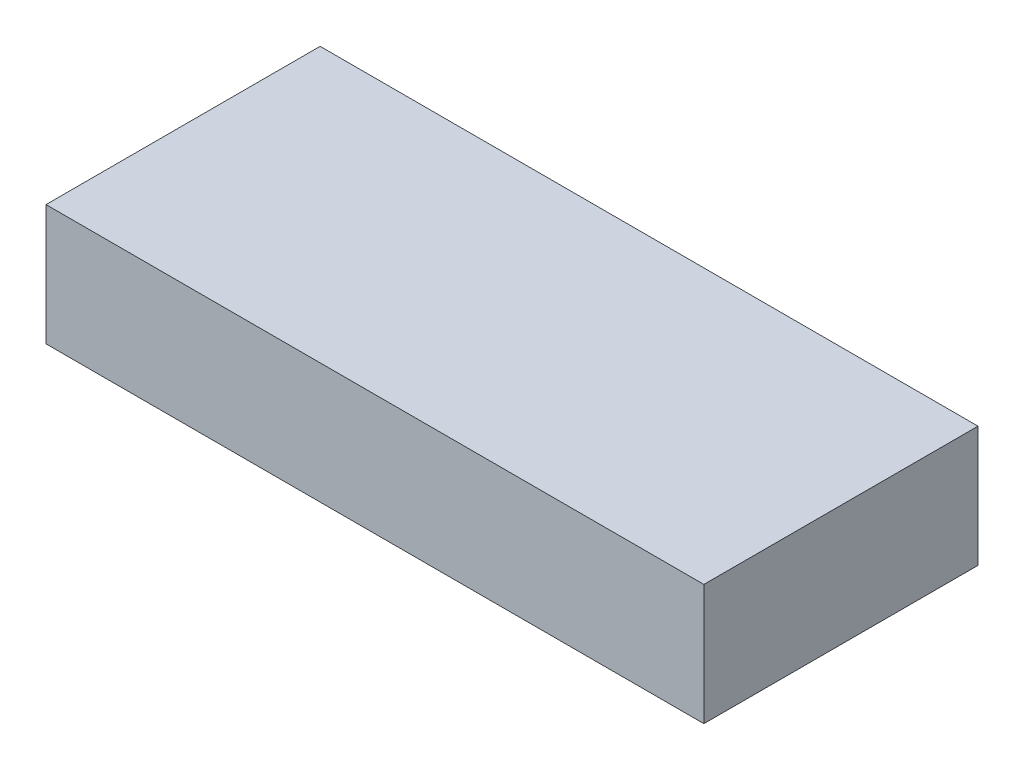
SolidWorks part; units mm, degrees
ref_plane "Front" through (0, 0, 0) normal (0, 0, 1) x (1, 0, 0)
ref_plane "Top" through (0, 0, 0) normal (0, 1, 0) x (1, 0, 0)
ref_plane "Right" through (0, 0, 0) normal (1, 0, 0) x (0, 0, -1)
sketch "Sketch1" plane through (0, 0, 0) normal (0, 1, 0) x (1, 0, 0)
  line L1 (0, 0) -> (60, 0)
  line L2 (0, 0) -> (0, -25)
  line L3 (0, -25) -> (60, -25)
  line L4 (60, 0) -> (60, -25)
  dimension "D1" = 60
  dimension "D2" = 25
extrude "Boss-Extrude1" add sketch "Sketch1" along normal blind 11
